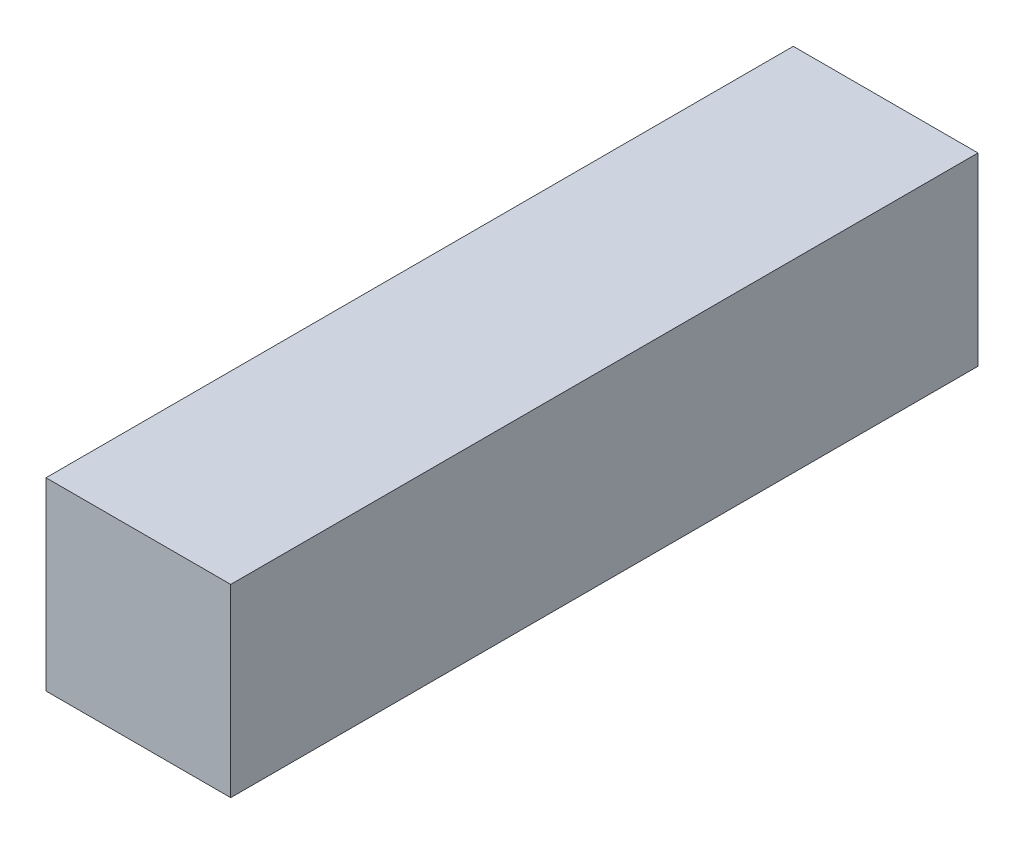
SolidWorks part; units mm, degrees
ref_plane "Face" through (0, 0, 0) normal (0, 0, 1) x (1, 0, 0)
ref_plane "Dessus" through (0, 0, 0) normal (0, 1, 0) x (1, 0, 0)
ref_plane "Droite" through (0, 0, 0) normal (1, 0, 0) x (0, 0, -1)
sketch "Esquisse1" plane through (0, 0, 0) normal (0, 0, 1) x (1, 0, 0)
  line L1 (0, 0) -> (22, 0)
  line L2 (0, 0) -> (0, 22)
  line L3 (0, 22) -> (22, 22)
  line L4 (22, 0) -> (22, 22)
  dimension "D1" = 22
  dimension "D2" = 22
extrude "Extrusion1" add sketch "Esquisse1" against normal blind 89
